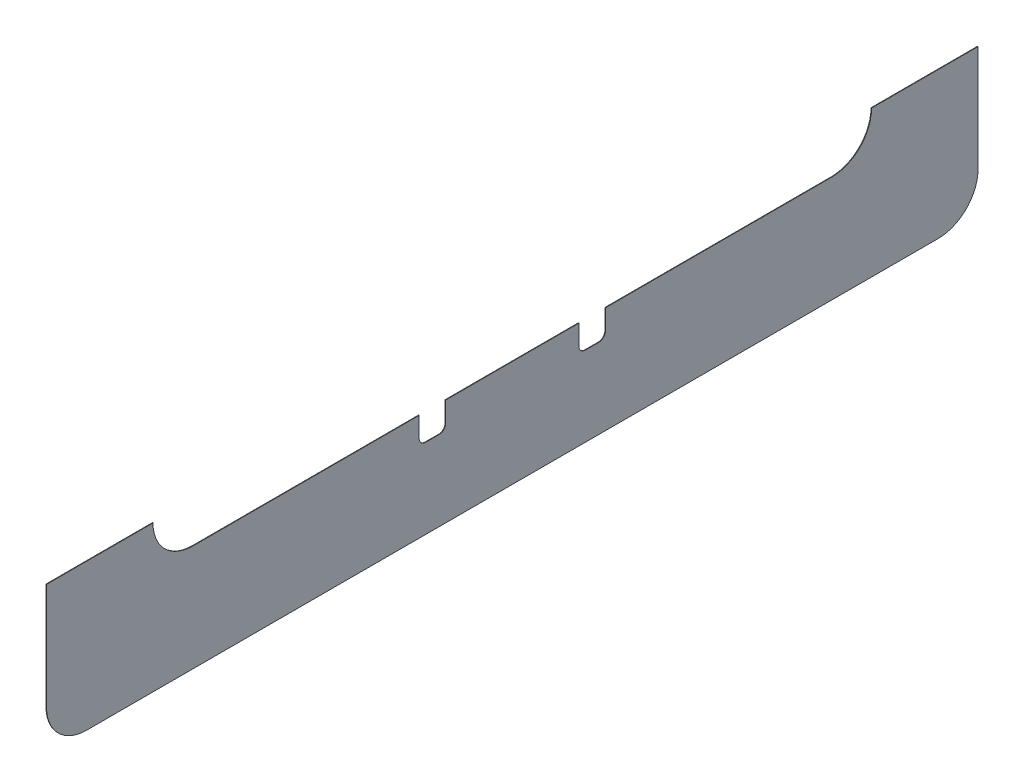
SolidWorks part; units mm, degrees
material "Delrin 2700 NC010, Low Viscosity Acetal Copolymer (SS)"
ref_plane "Front Plane" through (0, 0, 0) normal (0, 0, 1) x (1, 0, 0)
ref_plane "Top Plane" through (0, 0, 0) normal (0, 1, 0) x (1, 0, 0)
ref_plane "Right Plane" through (0, 0, 0) normal (1, 0, 0) x (0, 0, -1)
sketch "Sketch1" plane through (0, 0, 0) normal (1, 0, 0) x (0, 0, -1)
  line L0 (-222.25, 0) -> (-171.45, 0)
  line L1 (-165.1, 0) -> (165.1, 0) construction
  line L2 (-165.1, 0) -> (-165.1, -228.6) construction
  line L3 (-165.1, -228.6) -> (165.1, -228.6) construction
  line L4 (165.1, 0) -> (165.1, -228.6) construction
  line L5 (171.45, 0) -> (222.25, 0)
  line L6 (-171.45, 0) -> (-171.45, -215.9)
  line L7 (-152.4, -234.95) -> (152.4, -234.95)
  line L8 (171.45, 0) -> (171.45, -215.9)
  line L9 (-165.1, 0) -> (-165.1, 25.4) construction
  line L10 (-222.25, 0) -> (-222.25, -266.7)
  line L11 (-203.2, -285.75) -> (203.2, -285.75)
  line L12 (222.25, 0) -> (222.25, -266.7)
  line L13 (-165.1, 25.4) -> (165.1, 25.4) construction
  line L14 (165.1, 25.4) -> (165.1, 0) construction
  line L15 (0, -234.95) -> (0, -285.75) construction
  arc A0 (203.2, -285.75) -> (222.25, -266.7) centre (203.2, -266.7) ccw
  arc A1 (-203.2, -285.75) -> (-222.25, -266.7) centre (-203.2, -266.7) cw
  arc A2 (171.45, -215.9) -> (152.4, -234.95) centre (152.4, -215.9) cw
  arc A3 (-152.4, -234.95) -> (-171.45, -215.9) centre (-152.4, -215.9) cw
  dimension "D8" = 19.05
  dimension "D1" = 50.8
  dimension "D2" = 330.2
  dimension "D3" = 228.6
  dimension "D4" = 6.35
  dimension "D5" = 6.35
  dimension "D6" = 6.35
  dimension "D7" = 50.8
  dimension "D9" = 254
  dimension "D10" = 25.4
  dimension "D11" = 285.75
extrude "Boss-Extrude2" add sketch "Sketch1" along normal blind 0.254 contours L8 A2 L7 L15 L11 A0 L12 L5
sketch "Sketch11" plane through (0, 0, 0) normal (-1, 0, 0) x (0, 0, 1)
  line L0 (-171.45, 0) -> (-171.45, -215.9) construction
  line L1 (-171.45, -103.759) -> (-180.975, -103.759)
  line L2 (-171.45, -103.759) -> (-171.45, -136.779)
  line L3 (-171.45, -136.779) -> (-180.975, -136.779)
  line L4 (-184.15, -106.934) -> (-184.15, -133.604)
  line L5 (0, 0) -> (0, -234.95) construction
  line L6 (-171.45, -120.269) -> (-171.45, 0) construction
  line L7 (152.4, -234.95) -> (-152.4, -234.95) construction
  line L8 (-44.45, -234.95) -> (-31.75, -234.95)
  line L9 (-44.45, -234.95) -> (-44.45, -244.475)
  line L10 (-41.275, -247.65) -> (-34.925, -247.65)
  line L11 (-31.75, -234.95) -> (-31.75, -244.475)
  line L13 (-38.1, -234.95) -> (0, -234.95) construction
  arc A0 (-180.975, -136.779) -> (-184.15, -133.604) centre (-180.975, -133.604) cw
  arc A1 (-184.15, -106.934) -> (-180.975, -103.759) centre (-180.975, -106.934) cw
  arc A2 (-34.925, -247.65) -> (-31.75, -244.475) centre (-34.925, -244.475) ccw
  arc A3 (-41.275, -247.65) -> (-44.45, -244.475) centre (-41.275, -244.475) cw
  point P10 (-184.15, -136.779)
  point P13 (-184.15, -103.759)
  point P25 (-31.75, -247.65)
  point P28 (-44.45, -247.65)
  dimension "D4" = 3.175
  dimension "D8" = 3.175
  dimension "D1" = 12.7
  dimension "D2" = 33.02
  dimension "D3" = 120.269
  dimension "D5" = 12.7
  dimension "D6" = 12.7
  dimension "D7" = 38.1
extrude "Cut-Extrude1" cut sketch "Sketch11" against normal through all
mirror "Mirror2" about plane through (0, 0, 0) normal (0, 0, 1) of "Cut-Extrude1"
sketch "Sketch13" plane through (0, 0, 0) normal (-1, 0, 0) x (0, 0, 1)
  line L0 (222.25, 0) -> (222.25, -266.7) construction
  line L1 (-222.25, 0) -> (222.25, 0)
  line L2 (-222.25, 0) -> (-222.25, -215.9)
  line L3 (-222.25, -215.9) -> (222.25, -215.9)
  line L4 (222.25, 0) -> (222.25, -215.9)
  line L5 (203.2, -285.75) -> (-203.2, -285.75) construction
  dimension "D1" = 69.85
extrude "Cut-Extrude3" cut sketch "Sketch13" against normal through all
